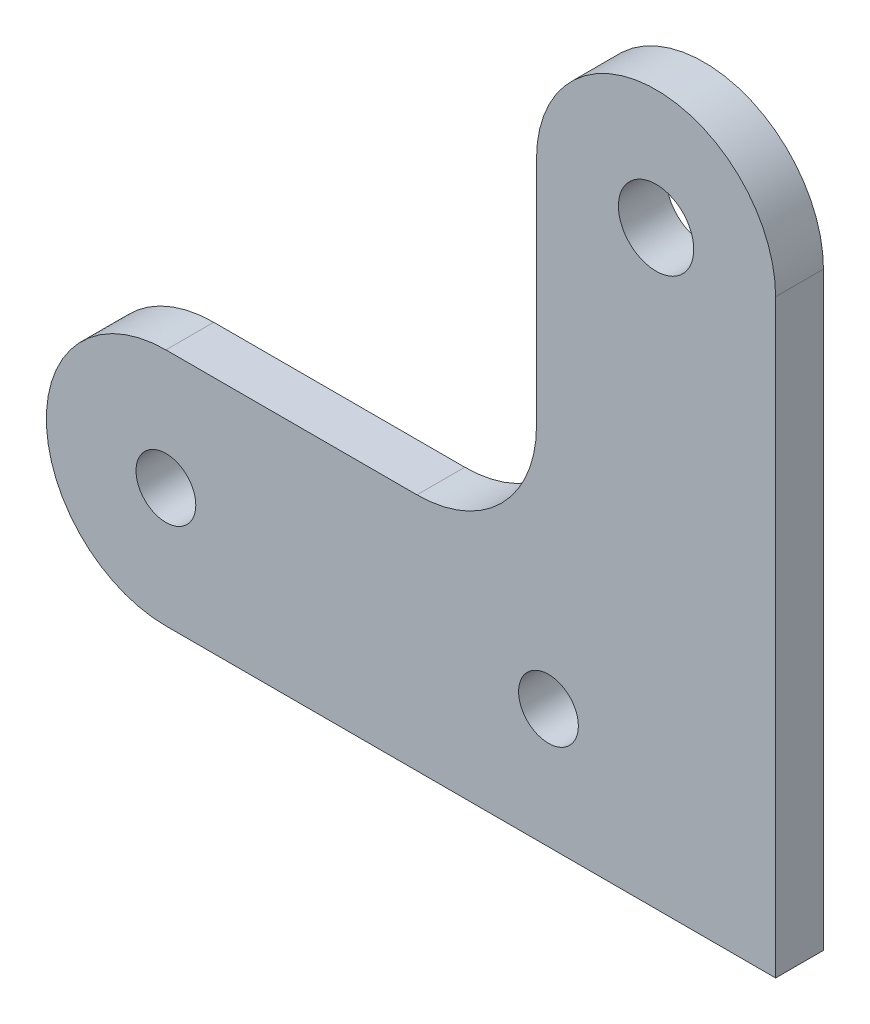
SolidWorks part; units mm, degrees
ref_plane "前视基准面" through (0, 0, 0) normal (0, 0, 1) x (1, 0, 0)
ref_plane "上视基准面" through (0, 0, 0) normal (0, 1, 0) x (1, 0, 0)
ref_plane "右视基准面" through (0, 0, 0) normal (1, 0, 0) x (0, 0, -1)
sketch "草图1" plane through (0, 0, 0) normal (0, 0, 1) x (1, 0, 0)
  line L0 (-1, 2.2913) -> (-1, -2.2913)
  line L1 (-32, 10) -> (-11, 10)
  line L2 (-32, 2.5) -> (-32, -2.5)
  line L3 (-32, -10) -> (19, -10)
  line L5 (5.85, 39.35) -> (12.15, 39.35)
  line L6 (-1, 39.35) -> (-1, 20)
  line L7 (-1, -10) -> (19, -10)
  line L8 (19, 39.35) -> (19, -10)
  circle A0 centre (0, 0) radius 2.5
  circle A1 centre (9, 39.35) radius 3.15
  circle A2 centre (-32, 0) radius 2.5
  arc A3 (-32, 10) -> (-32, -10) centre (-32, 0) ccw
  arc A4 (19, 39.35) -> (-1, 39.35) centre (9, 39.35) ccw
  arc A5 (-11, 10) -> (-1, 20) centre (-11, 20) ccw
  dimension "D1" = 5
  dimension "D2" = 5
  dimension "D3" = 6.3
  dimension "D4" = 9
  dimension "D5" = 39.35
  dimension "D6" = 32
  dimension "D7" = 20
  dimension "D8" = 20
  dimension "D9" = 10
extrude "凸台-拉伸1" add sketch "草图1" along normal blind 4 contours A5 L1 A3 L3 L8 A4 L6 A2 A1 A0
